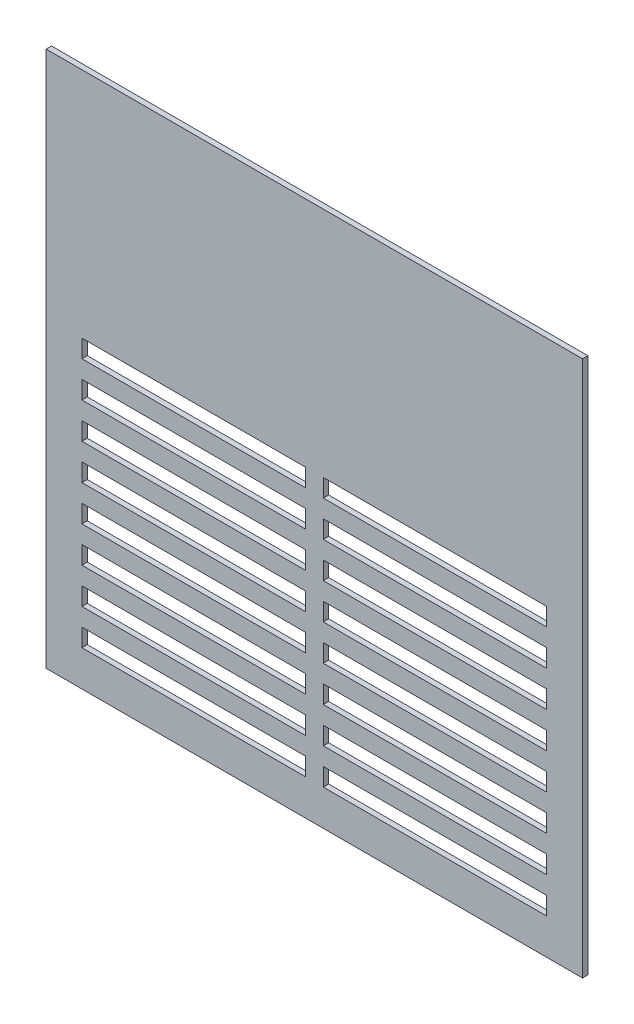
SolidWorks part; units mm, degrees
ref_plane "Alzado" through (0, 0, 0) normal (0, 0, 1) x (1, 0, 0)
ref_plane "Planta" through (0, 0, 0) normal (0, 1, 0) x (1, 0, 0)
ref_plane "Vista lateral" through (0, 0, 0) normal (1, 0, 0) x (0, 0, -1)
sketch "Croquis1" plane through (0, 0, 0) normal (0, 0, 1) x (1, 0, 0)
  line L6 (0, 0) -> (300, 0)
  line L7 (0, 0) -> (0, 300)
  line L8 (0, 300) -> (300, 300)
  line L9 (300, 0) -> (300, 300)
  dimension "D1" = 300
  dimension "D2" = 300
extrude "Saliente-Extruir1" add sketch "Croquis1" along normal blind 3
sketch "Croquis2" plane through (0, 0, 3) normal (0, 0, 1) x (1, 0, 0)
  line L0 (0, 300) -> (0, 0) construction
  line L1 (20, 20) -> (145, 20)
  line L2 (20, 20) -> (20, 30)
  line L3 (20, 170) -> (145, 170)
  line L5 (20, 160) -> (20, 170)
  line L6 (0, 0) -> (300, 0) construction
  line L7 (20, 160) -> (145, 160)
  line L8 (20, 150) -> (145, 150)
  line L9 (20, 140) -> (145, 140)
  line L10 (20, 130) -> (145, 130)
  line L11 (20, 120) -> (145, 120)
  line L12 (20, 110) -> (145, 110)
  line L13 (20, 100) -> (145, 100)
  line L14 (20, 90) -> (145, 90)
  line L15 (20, 80) -> (145, 80)
  line L16 (20, 70) -> (145, 70)
  line L17 (20, 60) -> (145, 60)
  line L18 (20, 50) -> (145, 50)
  line L19 (20, 40) -> (145, 40)
  line L20 (20, 30) -> (145, 30)
  line L22 (145, 170) -> (145, 160)
  line L23 (20, 140) -> (20, 150)
  line L24 (20, 120) -> (20, 130)
  line L25 (20, 100) -> (20, 110)
  line L26 (20, 80) -> (20, 90)
  line L27 (20, 60) -> (20, 70)
  line L28 (20, 40) -> (20, 50)
  line L29 (145, 150) -> (145, 140)
  line L30 (145, 130) -> (145, 120)
  line L31 (145, 110) -> (145, 100)
  line L32 (145, 90) -> (145, 80)
  line L33 (145, 70) -> (145, 60)
  line L34 (145, 50) -> (145, 40)
  line L35 (145, 30) -> (145, 20)
  line L36 (150, 0) -> (150, 300) construction
  line L37 (300, 300) -> (0, 300) construction
  line L38 (155, 30) -> (155, 20)
  line L39 (155, 50) -> (155, 40)
  line L40 (155, 70) -> (155, 60)
  line L41 (155, 90) -> (155, 80)
  line L42 (155, 110) -> (155, 100)
  line L43 (155, 130) -> (155, 120)
  line L44 (155, 150) -> (155, 140)
  line L45 (280, 40) -> (280, 50)
  line L46 (280, 60) -> (280, 70)
  line L47 (280, 80) -> (280, 90)
  line L48 (280, 100) -> (280, 110)
  line L49 (280, 120) -> (280, 130)
  line L50 (280, 140) -> (280, 150)
  line L51 (155, 170) -> (155, 160)
  line L52 (280, 30) -> (155, 30)
  line L53 (280, 40) -> (155, 40)
  line L54 (280, 50) -> (155, 50)
  line L55 (280, 60) -> (155, 60)
  line L56 (280, 70) -> (155, 70)
  line L57 (280, 80) -> (155, 80)
  line L58 (280, 90) -> (155, 90)
  line L59 (280, 100) -> (155, 100)
  line L60 (280, 110) -> (155, 110)
  line L61 (280, 120) -> (155, 120)
  line L62 (280, 130) -> (155, 130)
  line L63 (280, 140) -> (155, 140)
  line L64 (280, 150) -> (155, 150)
  line L65 (280, 160) -> (155, 160)
  line L66 (280, 160) -> (280, 170)
  line L67 (280, 170) -> (155, 170)
  line L68 (280, 20) -> (280, 30)
  line L69 (280, 20) -> (155, 20)
  dimension "D1" = 20
  dimension "D3" = 150
  dimension "D4" = 20
  dimension "D5" = 15
extrude "Cortar-Extruir1" cut sketch "Croquis2" against normal blind 10
